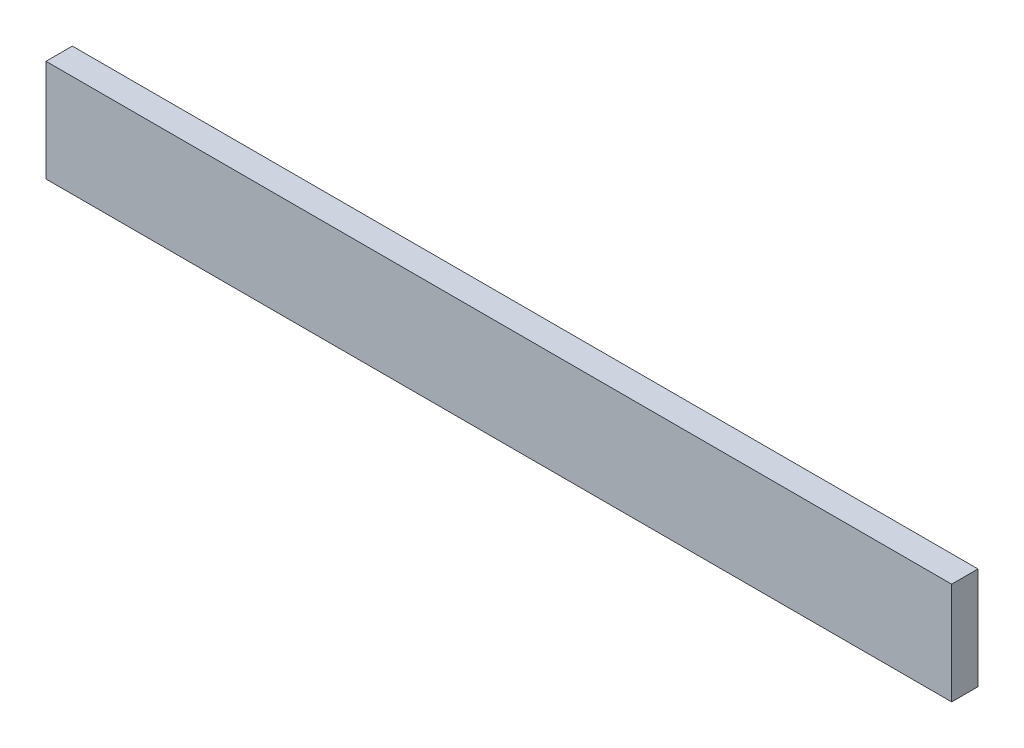
SolidWorks part; units mm, degrees
ref_plane "Front Plane" through (0, 0, 0) normal (0, 0, 1) x (1, 0, 0)
ref_plane "Top Plane" through (0, 0, 0) normal (0, 1, 0) x (1, 0, 0)
ref_plane "Right Plane" through (0, 0, 0) normal (1, 0, 0) x (0, 0, -1)
sketch "Sketch1" plane through (0, 0, 0) normal (0, 0, 1) x (1, 0, 0)
  line L1 (-275, 30.97) -> (275, 30.97)
  line L2 (-275, 30.97) -> (-275, -30.97)
  line L3 (-275, -30.97) -> (275, -30.97)
  line L4 (275, 30.97) -> (275, -30.97)
  point P4 (-275, 0)
  point P5 (0, -30.97)
  dimension "D1" = 61.94
  dimension "D2" = 550
extrude "Boss-Extrude1" add sketch "Sketch1" along normal blind 16
